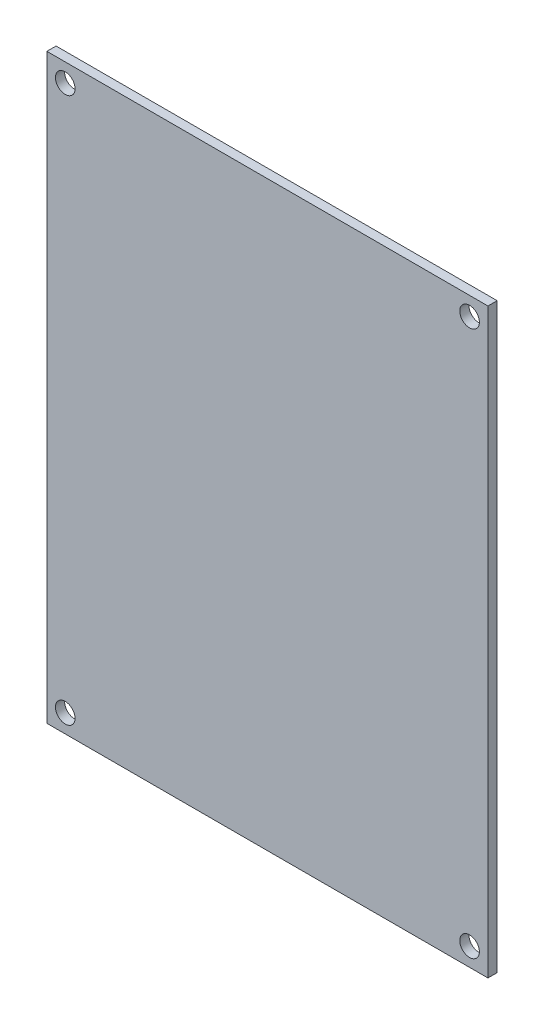
SolidWorks part; units mm, degrees
material "ABS"
ref_plane "正面" through (0, 0, 0) normal (0, 0, 1) x (1, 0, 0)
ref_plane "平面" through (0, 0, 0) normal (0, 1, 0) x (1, 0, 0)
ref_plane "右側面" through (0, 0, 0) normal (1, 0, 0) x (0, 0, -1)
sketch "ｽｹｯﾁ1" plane through (0, 0, 0) normal (0, 0, 1) x (1, 0, 0)
  line L1 (36, -47.5) -> (-36, -47.5)
  line L2 (36, -47.5) -> (36, 47.5)
  line L3 (36, 47.5) -> (-36, 47.5)
  line L4 (-36, -47.5) -> (-36, 47.5)
  line L5 (36, -47.5) -> (-36, 47.5) construction
  line L6 (36, 47.5) -> (-36, -47.5) construction
  line L7 (33, -44.5) -> (-33, -44.5) construction
  line L8 (33, -44.5) -> (33, 44.5) construction
  line L9 (33, 44.5) -> (-33, 44.5) construction
  line L10 (-33, -44.5) -> (-33, 44.5) construction
  line L11 (33, -44.5) -> (-33, 44.5) construction
  line L12 (33, 44.5) -> (-33, -44.5) construction
  circle A0 centre (-33, 44.5) radius 1.6
  circle A1 centre (33, 44.5) radius 1.6
  circle A2 centre (-33, -44.5) radius 1.6
  circle A3 centre (33, -44.5) radius 1.6
  point P0 (0, 0)
  point P6 (0, 0)
  dimension "D3" = 3.2
  dimension "D1" = 95
  dimension "D2" = 72
  dimension "D4" = 66
  dimension "D5" = 89
extrude "ﾎﾞｽ - 押し出し1" add sketch "ｽｹｯﾁ1" along normal blind 1.5
